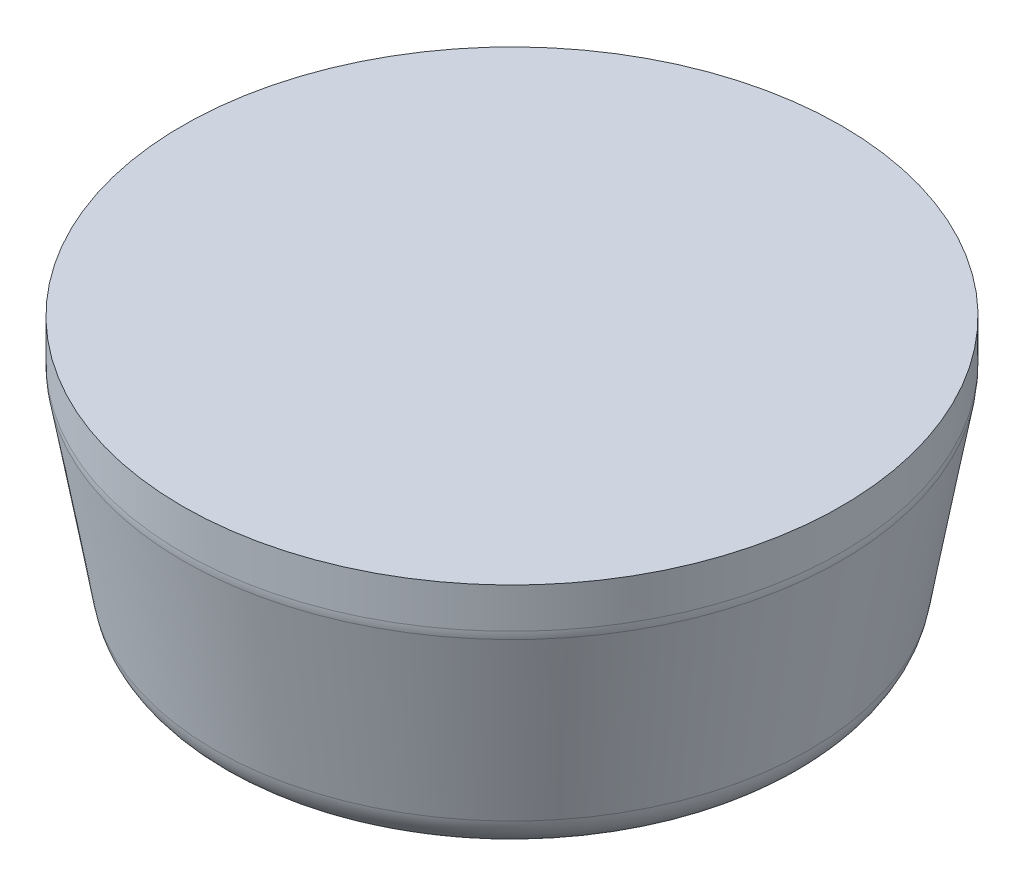
SolidWorks part; units mm, degrees
ref_plane "Front Plane" through (0, 0, 0) normal (0, 0, 1) x (1, 0, 0)
ref_plane "Top Plane" through (0, 0, 0) normal (0, 1, 0) x (1, 0, 0)
ref_plane "Right Plane" through (0, 0, 0) normal (1, 0, 0) x (0, 0, -1)
sketch "Sketch2" plane through (0, 0, 0) normal (0, 1, 0) x (1, 0, 0)
  circle A0 centre (0, 0) radius 7.5
  dimension "D1" = 15
extrude "Boss-Extrude1" add sketch "Sketch2" against normal blind 5 draft 10
sketch "Sketch3" plane through (0, 0, 0) normal (0, 1, 0) x (1, 0, 0)
  circle A1 centre (0, 0) radius 7.5
  circle A2 centre (0, 0) radius 7.5
  dimension "D1" = 0
extrude "Boss-Extrude2" add sketch "Sketch3" along normal blind 1
fillet "Fillet1" radius 1 2 edges at (0, 0, 7.5) (0, -5, 6.6184)
